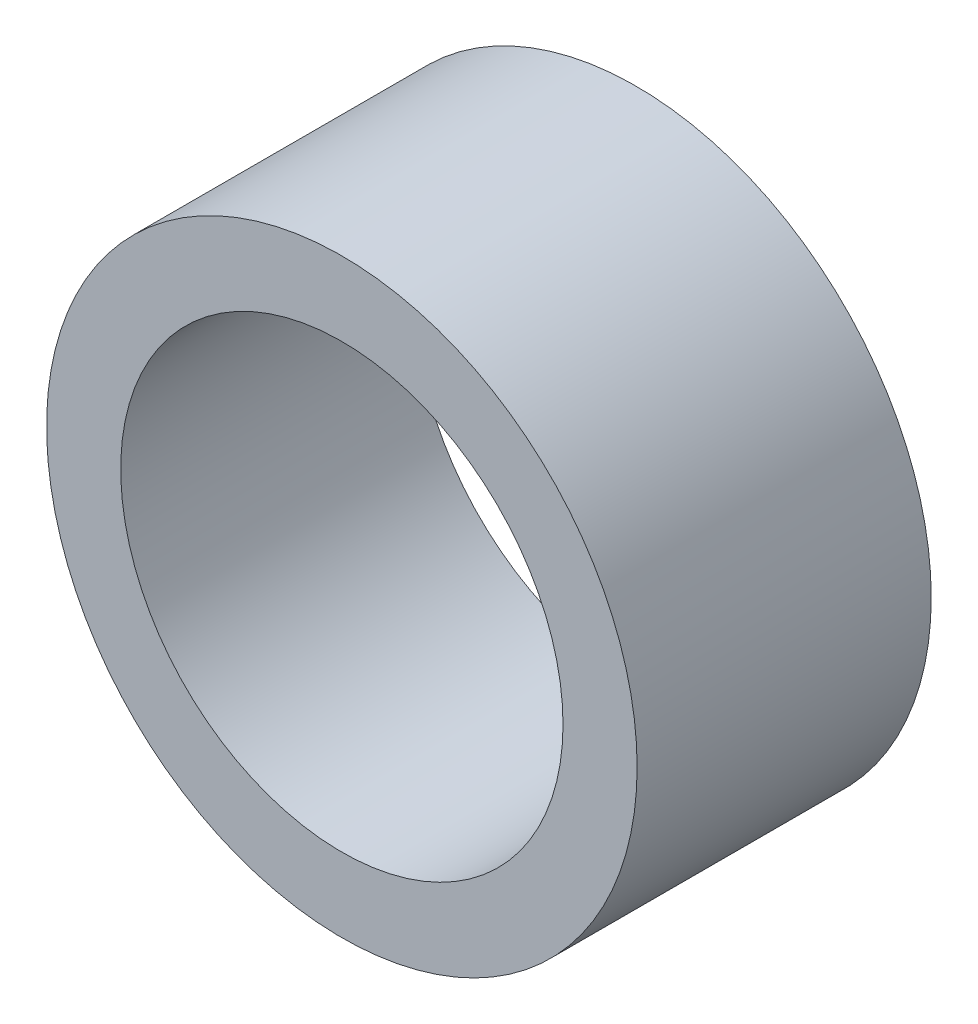
SolidWorks part; units mm, degrees
material "Brass"
ref_plane "Front Plane" through (0, 0, 0) normal (0, 0, 1) x (1, 0, 0)
ref_plane "Top Plane" through (0, 0, 0) normal (0, 1, 0) x (1, 0, 0)
ref_plane "Right Plane" through (0, 0, 0) normal (1, 0, 0) x (0, 0, -1)
sketch "Sketch1" plane through (0, 0, 0) normal (0, 0, 1) x (1, 0, 0)
  circle A0 centre (0, 0) radius 6.3754
  circle A1 centre (0, 0) radius 4.7752
  dimension "ID" = 9.5504
  dimension "OD" = 12.7508
extrude "Boss-Extrude1" add sketch "Sketch1" along normal mid plane 6.35
sketch "Sketch2" plane through (0, 0, 0) normal (1, 0, 0) x (0, 0, -1)
  line L0 (-3.175, 6.3754) -> (3.175, 6.3754)
  line L1 (-3.175, 0) -> (3.175, 0) construction
  line L2 (-3.175, 6.3754) -> (-3.175, -6.3754) construction
  line L3 (3.175, -6.3754) -> (3.175, 6.3754) construction
  dimension "D1" = 12.7508
  dimension "D2" = 6.35
equation "\"D1@Sketch2\"=\"OD@Sketch1\""
